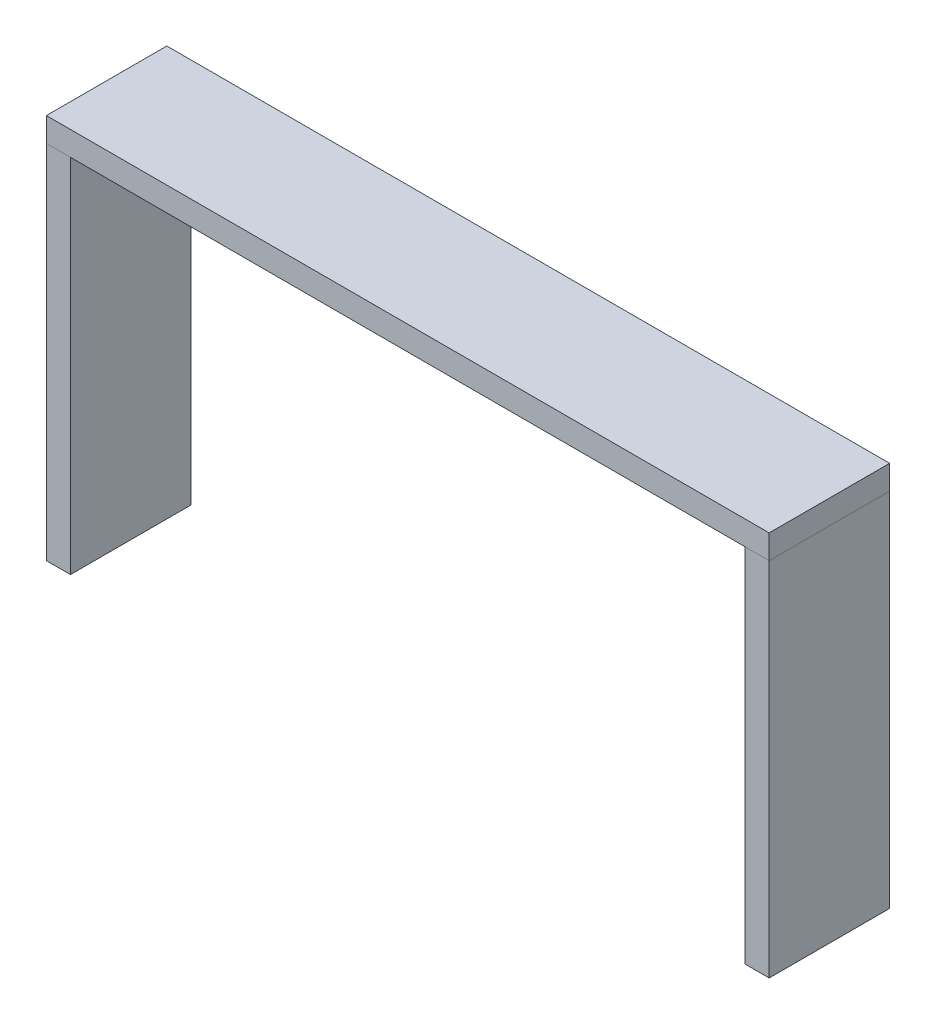
SolidWorks part; units mm, degrees
ref_plane "Front Plane" through (0, 0, 0) normal (0, 0, 1) x (1, 0, 0)
ref_plane "Top Plane" through (0, 0, 0) normal (0, 1, 0) x (1, 0, 0)
ref_plane "Right Plane" through (0, 0, 0) normal (1, 0, 0) x (0, 0, -1)
sketch "Sketch1" plane through (0, 0, 0) normal (0, 1, 0) x (1, 0, 0)
  line L0 (0, 50) -> (0, -50) construction
  line L1 (-280, -50) -> (-300, -50)
  line L2 (-280, -50) -> (-280, 50)
  line L3 (-280, 50) -> (-300, 50)
  line L4 (-300, -50) -> (-300, 50)
  line L5 (-280, -50) -> (-300, 50) construction
  line L6 (-280, 50) -> (-300, -50) construction
  line L7 (280, 50) -> (300, 50)
  line L8 (300, -50) -> (300, 50)
  line L9 (280, -50) -> (300, -50)
  line L10 (280, -50) -> (280, 50)
  point P0 (-290, 0)
  dimension "D1" = 100
  dimension "D2" = 20
  dimension "D3" = 600
extrude "Boss-Extrude1" add sketch "Sketch1" along normal blind 300
sketch "Sketch2" plane through (0, 300, 0) normal (0, 1, 0) x (1, 0, 0)
  line L1 (-300, 50) -> (300, 50)
  line L2 (-300, 50) -> (-300, -50)
  line L3 (-300, -50) -> (300, -50)
  line L4 (300, 50) -> (300, -50)
extrude "Boss-Extrude2" add sketch "Sketch2" along normal blind 20 separate body
